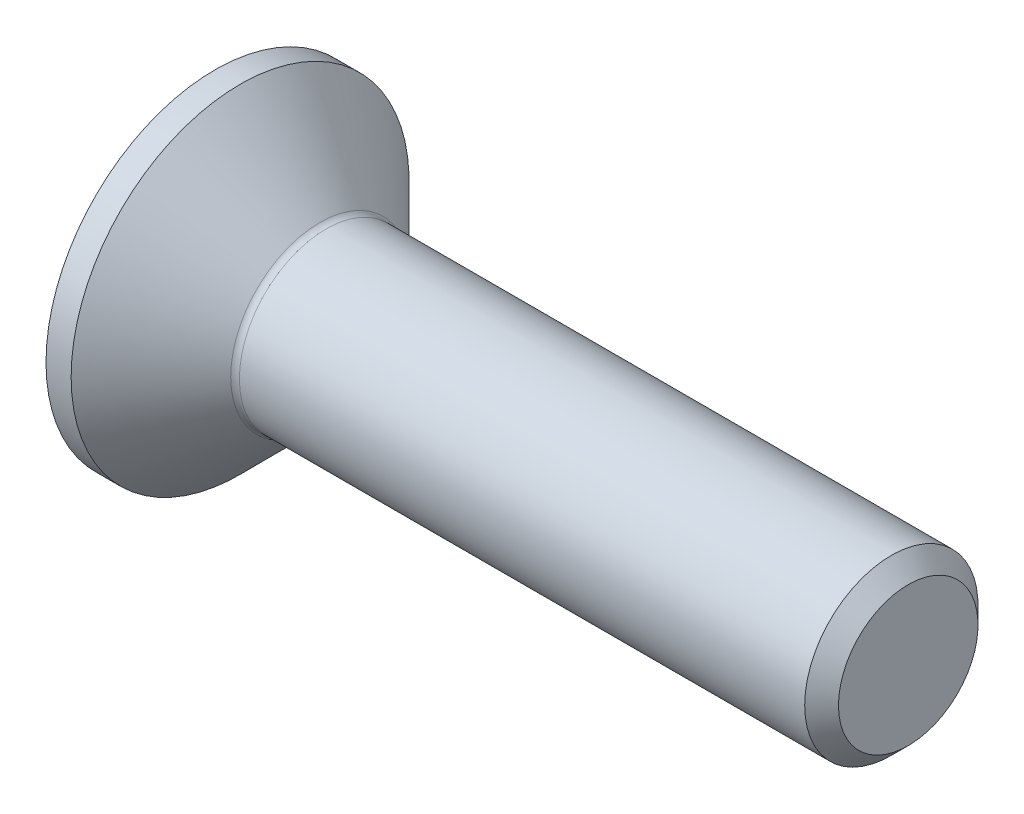
SolidWorks part; units mm, degrees
ref_plane "Plane1" through (0, 0, 0) normal (0, 0, 1) x (1, 0, 0)
ref_plane "Plane2" through (0, 0, 0) normal (0, 1, 0) x (1, 0, 0)
ref_plane "Plane3" through (0, 0, 0) normal (1, 0, 0) x (0, 0, -1)
sketch "BodySke" plane through (0, 0, 0) normal (0, 0, 1) x (1, 0, 0)
  line L0 (0, 0) -> (0, 3.9)
  line L1 (0.58, 3.9) -> (2.48, 2)
  line L2 (0, 3.9) -> (0.58, 3.9)
  line L3 (2.48, 2) -> (15.61, 2)
  line L4 (16, 1.61) -> (16, 0)
  line L5 (16, 0) -> (0, 0)
  line L6 (0, 0) -> (127, 0) construction
  line L7 (0.58, -3.9) -> (2.48, -2) construction
  line L8 (16, 1.61) -> (15.61, 2)
  line L9 (0, -3.9) -> (0.58, -3.9) construction
  line L10 (16, -1.61) -> (15.61, -2) construction
  line L11 (3.18, 8.35) -> (3.18, -13.875) construction
  line L12 (0, 19.05) -> (0, -3.175) construction
  dimension "D1" = 0.58
  dimension "Diameter" = 4
  dimension "Head_ht" = 2.48
  dimension "Length" = 16
  dimension "Body_ch_ang" = 45
  dimension "Head_dia" = 7.8
  dimension "Minor_dia" = 3.22
  dimension "Head_ang" = 90
  dimension "Advance" = 0.7
  dimension "Thread_nom" = 16
revolve "BaseBody" add sketch "BodySke" angle 360 about L6
cosmetic thread "ThreadCosmetic" [suppressed] parameters "Thread_length"=12.12, "Thread_minor"=3.22
fillet "Fillet1" radius 0.2 1 edges at (2.48, 0, 2)
sketch "Sketch2" plane through (0, 0, 0) normal (0, 0, 1) x (1, 0, 0)
  line L0 (0, 1.25) -> (1.5, 1.25)
  line L1 (1.5, 1.25) -> (2.2217, 0)
  line L2 (0, 0) -> (127, 0) construction
  line L3 (2.2217, 0) -> (0, 0)
  line L4 (0, 0) -> (0, 1.25)
  line L5 (0, -1.25) -> (1.5, -1.25) construction
  line L6 (0, 0) -> (47.625, 0) construction
  line L8 (0, 3.9) -> (0, -3.9) construction
  dimension "D2" = 60
  dimension "PreBroach_depth" = 1.5
  dimension "PreBroach_dia" = 2.5
revolve "PreBroach" cut sketch "Sketch2" angle 360 about L6
sketch "Sketch3" plane through (0, 0, 0) normal (-1, 0, 0) x (0, 0, 1)
  line L0 (-1.25, -0.7217) -> (-1.25, 0.7217)
  line L1 (-1.25, 0.7217) -> (0, 1.4434)
  line L2 (0, 1.4434) -> (1.25, 0.7217)
  line L3 (1.25, 0.7217) -> (1.25, -0.7217)
  line L4 (1.25, -0.7217) -> (0, -1.4434)
  line L5 (0, -1.4434) -> (-1.25, -0.7217)
  dimension "D1" = 1.25
  dimension "D2" = 1.25
  dimension "D3" = 2.5
  dimension "Hex_size" = 2.5
extrude "Hex" cut sketch "Sketch3" against normal blind 1.5
sketch "ThdSchSke" [suppressed] plane through (0, 0, 0) normal (0, 0, 1) x (1, 0, 0)
  line L0 (15.16, -8.626) -> (14.1979, -10)
  line L1 (15.16, -8.626) -> (16.1221, -10)
  line L2 (16.1221, -10) -> (16.1221, -12.5)
  line L3 (-3.175, 0) -> (5.1513, 0) construction
  line L4 (0, 18.025) -> (0, -18.025) construction
  line L5 (16.1221, -12.5) -> (14.1979, -12.5)
  line L6 (14.1979, -12.5) -> (14.1979, -10)
  dimension "Thread_minor" = 3.22
  dimension "Diameter" = 4
  dimension "Start" = 3.88
  dimension "SideAngle" = 55
  dimension "VeeAngle" = 70
  dimension "Overcut" = 5
revolve "ThreadSchematic" [suppressed] cut sketch "ThdSchSke" angle 360 about L3
pattern_linear "ThdSchPat" [suppressed]
equation "\"Thread_minor@ThreadCosmetic\"  =  \"Minor_dia@BodySke\""
equation "\"D1@Sketch3\" = \"Hex_size@Sketch3\" / 2"
equation "\"D2@Sketch3\" = \"D1@Sketch3\""
equation "\"D3@Sketch3\" = \"Hex_size@Sketch3\""
equation "\"Thread_length@ThreadCosmetic\" = ((sgn( (\"Length@BodySke\" - \"Advance@BodySke\" * 2.0 - \"Head_ht@BodySke\" ) - \"Thread_nom@BodySke\" )-1)*( (\"Length@BodySke\" - \"Advance@BodySke\" * 2.0 - \"Head_ht@BodySke\" ) - \"Thread_nom@BodySke\" ))/-2+ \"Thread_nom@BodySke\""
equation "\"Thread_minor@ThdSchSke\" = \"Minor_dia@BodySke\""
equation "\"Diameter@ThdSchSke\" = \"Diameter@BodySke\""
equation "\"Overcut@ThdSchSke\" = \"Diameter@BodySke\" * 1.25"
equation "\"Start@ThdSchSke\" = 0.000001 + \"Length@BodySke\" - \"Thread_length@ThreadCosmetic\"  '---Countersunk---"
equation "\"Num_threads@ThdSchPat\" = int( \"Thread_length@ThreadCosmetic\" / \"Advance@BodySke\" + 0.999 )  + 1"
equation "\"Advance@ThdSchPat\" = \"Thread_length@ThreadCosmetic\" /  (\"Num_threads@ThdSchPat\" - 1) 'relax it"
equation "\"Num_threads@ThdSchPat\" = \"Num_threads@ThdSchPat\" - sgn( \"Num_threads@ThdSchPat\" - 1) '---chamfered tips only---"
